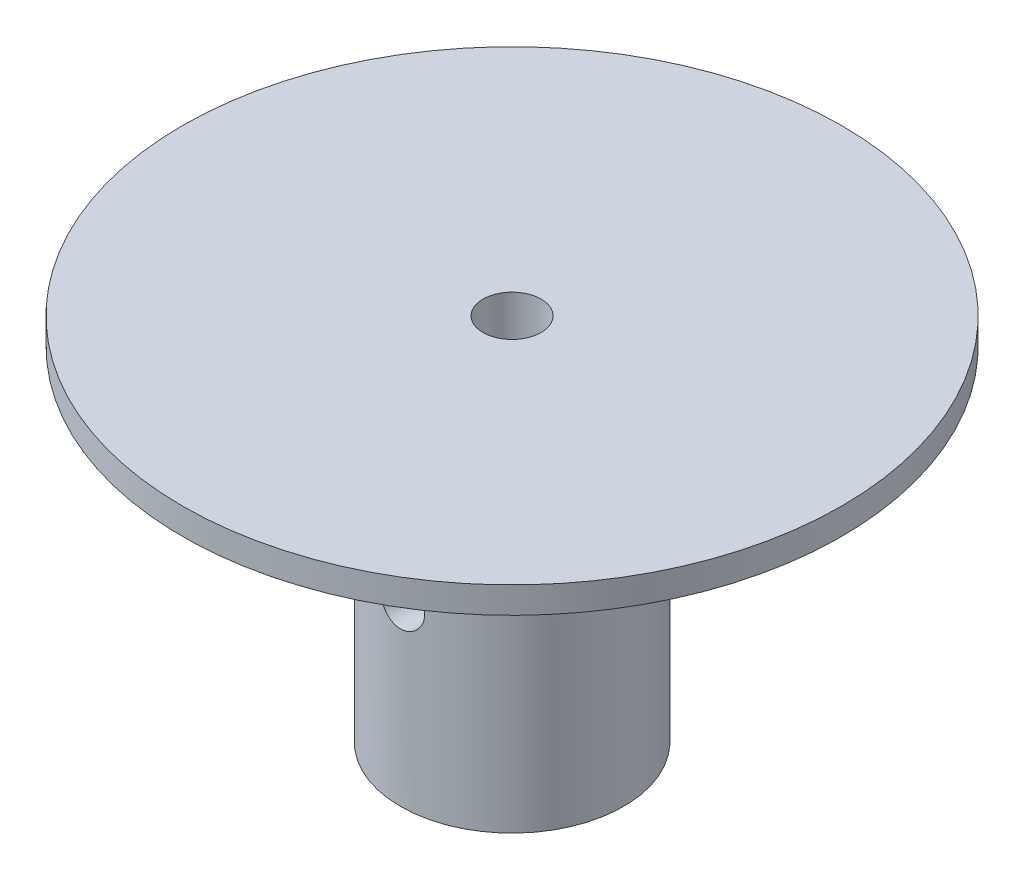
SolidWorks part; units mm, degrees
material "ABS"
ref_plane "Front Plane" through (0, 0, 0) normal (0, 0, 1) x (1, 0, 0)
ref_plane "Top Plane" through (0, 0, 0) normal (0, 1, 0) x (1, 0, 0)
ref_plane "Right Plane" through (0, 0, 0) normal (1, 0, 0) x (0, 0, -1)
sketch "Sketch1" plane through (0, 0, 0) normal (0, 1, 0) x (1, 0, 0)
  circle A0 centre (0, 0) radius 12.7
  dimension "D1" = 25.4
extrude "Boss-Extrude1" add sketch "Sketch1" along normal blind 40
sketch "Sketch2" plane through (0, 40, 0) normal (0, 1, 0) x (1, 0, 0)
  circle A0 centre (0, 0) radius 37.5
  dimension "D1" = 75
extrude "Boss-Extrude2" add sketch "Sketch2" along normal blind 2
fillet "Fillet1" [suppressed] radius 2.54
sketch "Sketch3" plane through (0, 0, 0) normal (0, -1, 0) x (-1, 0, 0)
  circle A0 centre (0, 0) radius 3.302
  dimension "D1" = 6.604
extrude "Cut-Extrude1" cut sketch "Sketch3" against normal through all
sketch "Sketch4" plane through (0, 0, 0) normal (0, 0, 1) x (1, 0, 0)
  line L0 (-37.5, 40) -> (37.5, 40) construction
  line L1 (-12.7, 40) -> (-12.7, 0) construction
  circle A0 centre (0, 20) radius 2.5
  dimension "D1" = 5
  dimension "D2" = 20
  dimension "D3" = 12.7
extrude "Cut-Extrude2" cut sketch "Sketch4" against normal through all and the other way through all
sketch "Sketch5" plane through (0, 40, 0) normal (0, -1, 0) x (1, 0, 0)
  circle A0 centre (0, 0) radius 12.7 construction
  circle A1 centre (0, 0) radius 37.5
  circle A2 centre (0, 0) radius 37.5
  circle A3 centre (0, 0) radius 12.7
  dimension "D1" = 0
extrude "Boss-Extrude3" add sketch "Sketch5" along normal blind 1
